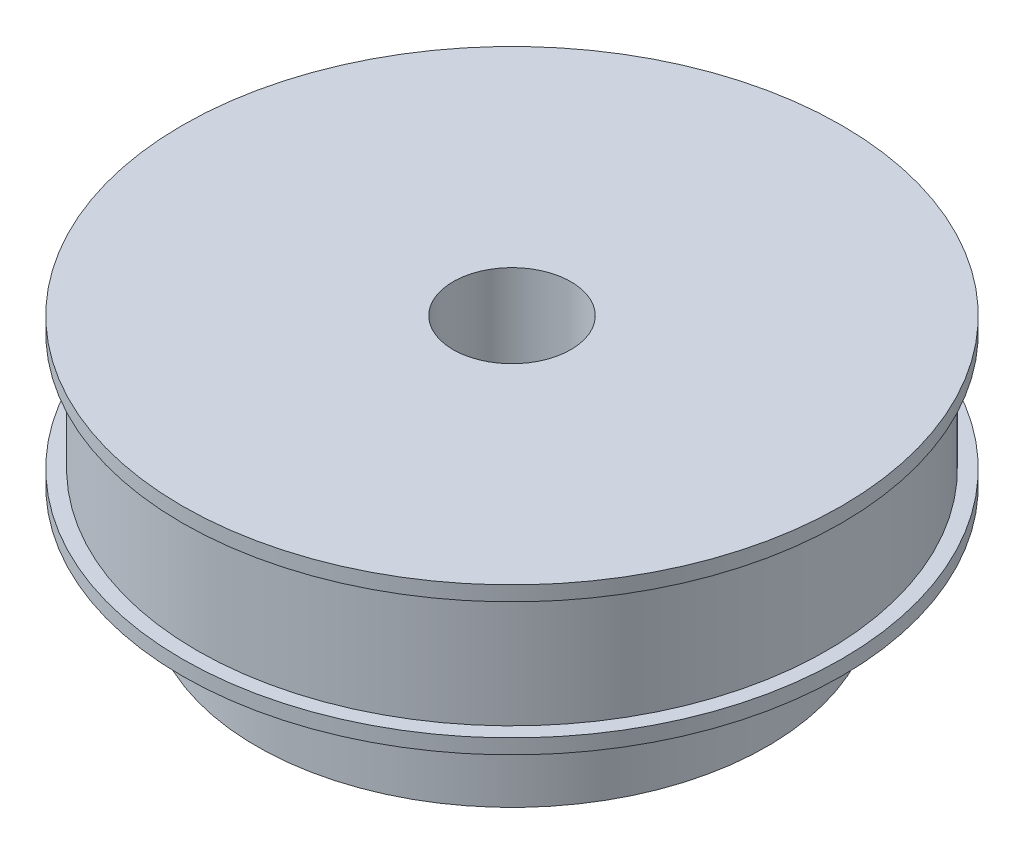
SolidWorks part; units mm, degrees
material "4032-T6"
ref_plane "Front Plane" through (0, 0, 0) normal (0, 0, 1) x (1, 0, 0)
ref_plane "Top Plane" through (0, 0, 0) normal (0, 1, 0) x (1, 0, 0)
ref_plane "Right Plane" through (0, 0, 0) normal (1, 0, 0) x (0, 0, -1)
sketch "Sketch1" plane through (0, 0, 0) normal (0, 1, 0) x (1, 0, 0)
  circle A0 centre (0, 0) radius 32.085
  dimension "D1" = 64.17
extrude "Boss-Extrude1" add sketch "Sketch1" along normal blind 12
sketch "Sketch3" plane through (0, 12, 0) normal (0, 1, 0) x (1, 0, 0)
  circle A0 centre (0, 0) radius 33.585
  dimension "D1" = 67.17
extrude "Boss-Extrude3" add sketch "Sketch3" along normal blind 1.5
sketch "Sketch4" plane through (0, 0, 0) normal (0, -1, 0) x (1, 0, 0)
  circle A0 centre (0, 0) radius 33.585
  dimension "D1" = 67.17
extrude "Boss-Extrude4" add sketch "Sketch4" along normal blind 1.5
sketch "Sketch5" plane through (0, -1.5, 0) normal (0, -1, 0) x (1, 0, 0)
  circle A0 centre (0, 0) radius 26
  dimension "D1" = 52
extrude "Boss-Extrude5" add sketch "Sketch5" along normal blind 10
sketch "Sketch6" plane through (0, 13.5, 0) normal (0, 1, 0) x (1, 0, 0)
  circle A0 centre (0, 0) radius 6
  dimension "D1" = 12
extrude "Cut-Extrude1" cut sketch "Sketch6" against normal up to surface (25 mm away) up to face at (0, -11.5, -26)
